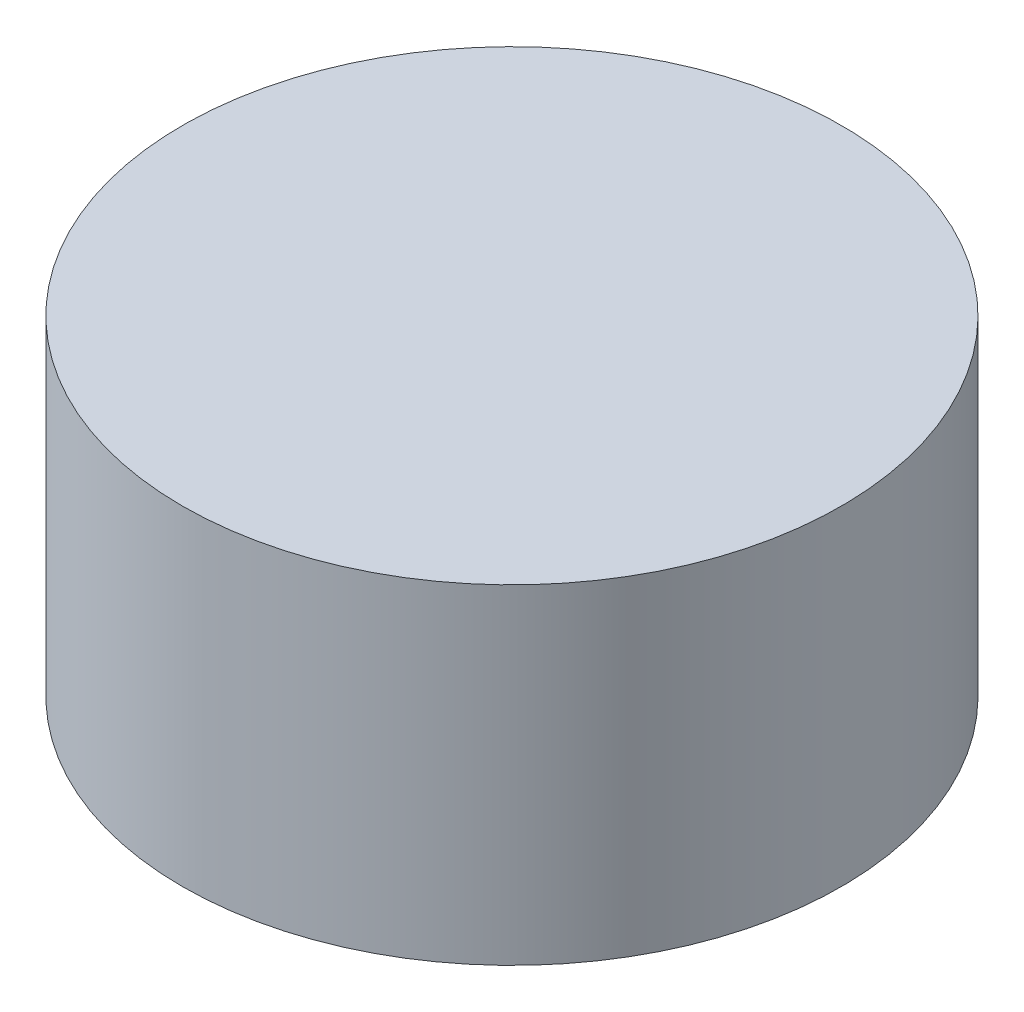
SolidWorks part; units mm, degrees
ref_plane "정면" through (0, 0, 0) normal (0, 0, 1) x (1, 0, 0)
ref_plane "윗면" through (0, 0, 0) normal (0, 1, 0) x (1, 0, 0)
ref_plane "우측면" through (0, 0, 0) normal (1, 0, 0) x (0, 0, -1)
sketch "스케치1" plane through (0, 0, 0) normal (0, 1, 0) x (1, 0, 0)
  circle A0 centre (0, 0) radius 6
  circle A1 centre (0, 0) radius 3
  dimension "D1" = 12
  dimension "D2" = 6
extrude "보스-돌출1" add sketch "스케치1" along normal blind 3 contours A0 | A1
sketch "스케치3" plane through (0, 3, 0) normal (0, 1, 0) x (1, 0, 0)
  circle A0 centre (0, 0) radius 6
extrude "보스-돌출2" add sketch "스케치3" along normal blind 3
